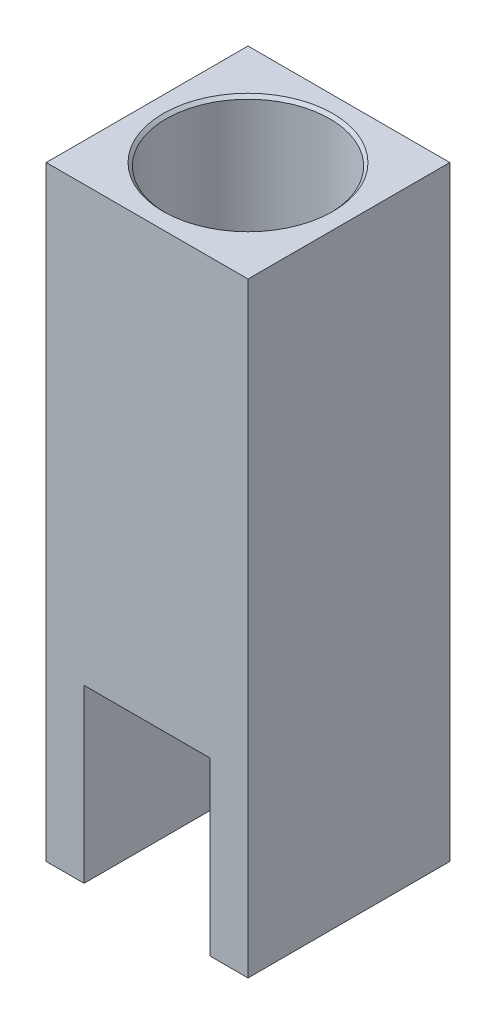
SolidWorks part; units mm, degrees
material "PC High Viscosity"
ref_plane "Front Plane" through (0, 0, 0) normal (0, 0, 1) x (1, 0, 0)
ref_plane "Top Plane" through (0, 0, 0) normal (0, 1, 0) x (1, 0, 0)
ref_plane "Right Plane" through (0, 0, 0) normal (1, 0, 0) x (0, 0, -1)
sketch "Sketch1" plane through (0, 0, 0) normal (0, 1, 0) x (1, 0, 0)
  line L1 (0, 0) -> (50.8, 0)
  line L2 (0, 0) -> (0, -50.8)
  line L3 (0, -50.8) -> (50.8, -50.8)
  line L4 (50.8, 0) -> (50.8, -50.8)
extrude "Boss-Extrude1" add sketch "Sketch1" along normal blind 152.4
sketch "Sketch2" plane through (0, 152.4, 0) normal (0, 1, 0) x (1, 0, 0)
  line L0 (0, 0) -> (0, -50.8) construction
  line L1 (50.8, 0) -> (0, 0) construction
  circle A0 centre (25.4, -25.4) radius 6.1468
  dimension "D1" = 25.4
  dimension "D2" = 25.4
extrude "Cut-Extrude1" cut sketch "Sketch2" against normal through all
sketch "Sketch3" plane through (0, 152.4, 0) normal (0, 1, 0) x (1, 0, 0)
  circle A0 centre (25.4, -25.4) radius 20.5994
extrude "Cut-Extrude2" cut sketch "Sketch3" against normal blind 74.93
sketch "Sketch4" plane through (0, 152.4, 0) normal (0, 1, 0) x (1, 0, 0)
  circle A0 centre (25.4, -25.4) radius 17.78
extrude "Cut-Extrude3" cut sketch "Sketch4" against normal blind 82.55
sketch "Sketch5" plane through (0, 0, 50.8) normal (0, 0, 1) x (1, 0, 0)
  line L0 (9.525, 0) -> (9.525, 36.83)
  line L1 (0, 0) -> (50.8, 0) construction
  line L2 (15.875, 43.18) -> (34.925, 43.18)
  line L3 (41.275, 36.83) -> (41.275, 0)
  line L4 (41.275, 0) -> (9.525, 0)
  line L5 (0, 152.4) -> (50.8, 152.4) construction
  line L6 (9.525, 36.83) -> (9.525, 43.18)
  line L7 (9.525, 43.18) -> (15.875, 43.18)
  line L8 (34.925, 43.18) -> (41.275, 43.18)
  line L9 (41.275, 43.18) -> (41.275, 36.83)
  point P5 (25.4, 0)
  point P9 (25.4, 152.4)
  point P12 (41.275, 43.18)
  point P15 (9.525, 43.18)
  dimension "D1" = 43.18
  dimension "D2" = 31.75
  dimension "D3" = 15.875
  dimension "D4" = 15.875
extrude "Cut-Extrude4" cut sketch "Sketch5" against normal blind 42.4434
sketch "Sketch6" plane through (0, 43.18, 0) normal (0, -1, 0) x (1, 0, 0)
  circle A0 centre (25.4, 25.4) radius 9.144
extrude "Cut-Extrude5" cut sketch "Sketch6" against normal blind 4.318
fillet "Fillet1" radius 6.35 2 edges at (9.525, 21.59, 8.3566) (41.275, 21.59, 8.3566)
sketch "Sketch7" plane through (0, 0, 0) normal (0, -1, 0) x (1, 0, 0)
  circle A0 centre (6.35, 6.35) radius 1.905
  circle A1 centre (44.45, 6.35) radius 1.905
  circle A2 centre (25.4, 25.4) radius 6.1468 construction
  circle A3 centre (25.4, 25.4) radius 9.144 construction
  dimension "D1" = 19.05
  dimension "D2" = 38.1
  dimension "D3" = 19.05
  dimension "D4" = 3.81
  dimension "D5" = 3.81
hole_wizard "#10-24 Tapped Hole1" positions "Sketch8" profile "Sketch9" tap size "#10-24" standard "ANSI Inch"
sketch "Sketch8" plane through (0, 0, 0) normal (0, -1, 0) x (-1, 0, 0)
  point P0 (-6.35, -6.35)
  point P3 (-44.45, -6.35)
sketch "Sketch9" plane through (6.35, 0, 6.35) normal (1, 0, 0) x (0, 0, -1)
  line L0 (0, 0) -> (0, 18.9208)
  line L1 (0, 18.9208) -> (1.8986, 17.78)
  line L2 (1.8986, 17.78) -> (1.8986, 0)
  line L5 (1.8986, 0) -> (0, 0)
  line L10 (0, 18.9208) -> (-1.8987, 17.78) construction
  line L11 (0, -6.35) -> (0, 107.95) construction
  dimension "Tap Drill Dia." = 3.7973
  dimension "Tap Drill Depth" = 17.78
  dimension "Drill Angle" = 118
cosmetic thread "Hole Thread1" parameters "D1"=9.652, "D2"=4.826
cosmetic thread "Hole Thread2" parameters "D1"=9.652, "D2"=4.826
chamfer "Chamfer1" distance 0.762 angle 45 1 edges at (25.4, 152.4, 45.9994)
